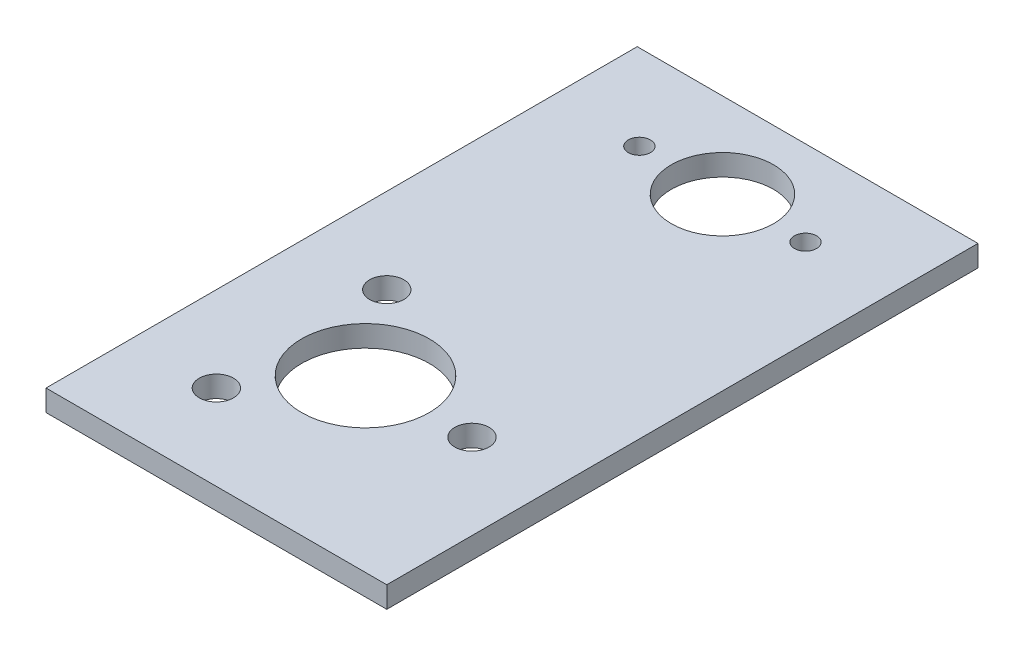
SolidWorks part; units mm, degrees
ref_plane "Front Plane" through (0, 0, 0) normal (0, 0, 1) x (1, 0, 0)
ref_plane "Top Plane" through (0, 0, 0) normal (0, 1, 0) x (1, 0, 0)
ref_plane "Right Plane" through (0, 0, 0) normal (1, 0, 0) x (0, 0, -1)
sketch "Sketch1" plane through (0, 0, 0) normal (0, 1, 0) x (1, 0, 0)
  line L1 (0, 0) -> (50.8, 0)
  line L2 (0, 0) -> (0, 88.138)
  line L3 (0, 88.138) -> (50.8, 88.138)
  line L4 (50.8, 0) -> (50.8, 88.138)
  dimension "D1" = 88.138
  dimension "D2" = 50.8
extrude "Boss-Extrude1" add sketch "Sketch1" along normal blind 3.175 contours L2 L3 L4 L1
sketch "Sketch2" plane through (0, 3.175, 0) normal (0, 1, 0) x (1, 0, 0)
  line L0 (0, 0) -> (0, 88.138) construction
  line L1 (12.7, 12.7) -> (12.7, 38.1) construction
  line L2 (12.7, 25.4) -> (38.1, 25.4) construction
  line L3 (0, 0) -> (50.8, 0) construction
  circle A0 centre (12.7, 12.7) radius 2.5527
  circle A1 centre (12.7, 38.1) radius 2.5527
  circle A2 centre (38.1, 25.4) radius 2.5527
  circle A3 centre (22.225, 25.4) radius 9.525
  dimension "D3" = 5.1054
  dimension "D6" = 19.05
  dimension "D1" = 12.7
  dimension "D2" = 38.1
  dimension "D4" = 25.4
  dimension "D5" = 12.7
  dimension "D7" = 22.225
extrude "Cut-Extrude1" cut sketch "Sketch2" against normal blind 3.175
sketch "Sketch4" plane through (0, 3.175, 0) normal (0, 1, 0) x (1, 0, 0)
  line L0 (13.0175, 75.438) -> (37.7825, 75.438) construction
  line L3 (0, 88.138) -> (50.8, 88.138) construction
  circle A0 centre (13.0175, 75.438) radius 1.651
  circle A1 centre (37.7825, 75.438) radius 1.651
  circle A2 centre (25.4, 75.438) radius 7.62
  point P6 (25.4, 88.138)
  point P8 (25.4, 75.438)
  point P10 (25.4, 88.138)
  dimension "D1" = 3.302
  dimension "D3" = 15.24
  dimension "D2" = 24.765
  dimension "D4" = 12.7
extrude "Cut-Extrude2" cut sketch "Sketch4" against normal blind 3.175
